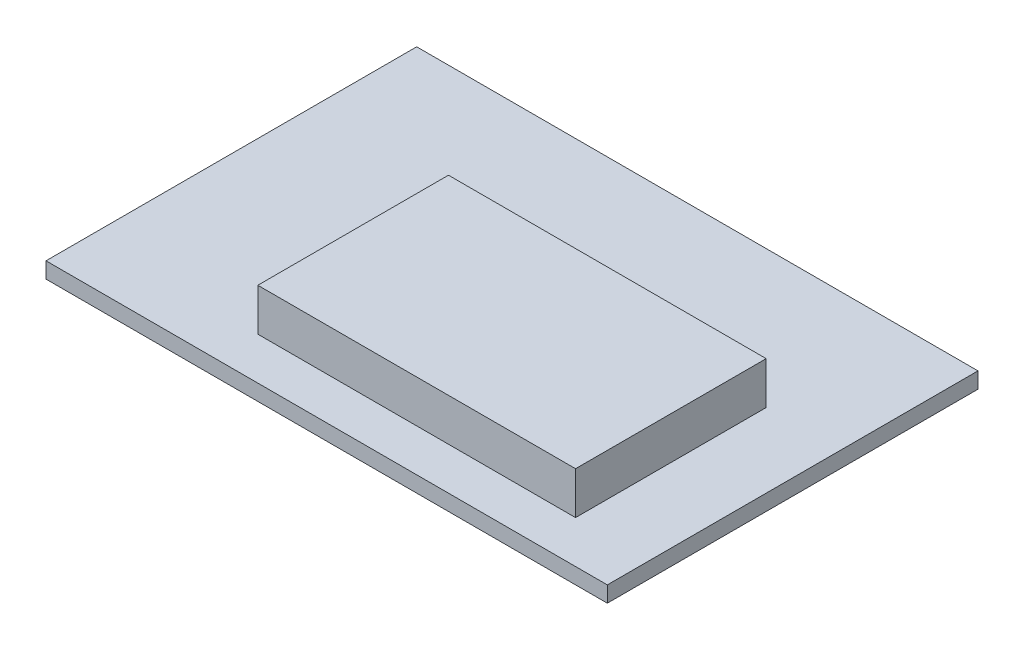
SolidWorks part; units mm, degrees
ref_plane "Frontal" through (0, 0, 0) normal (0, 0, 1) x (1, 0, 0)
ref_plane "Superior" through (0, 0, 0) normal (0, 1, 0) x (1, 0, 0)
ref_plane "Direito" through (0, 0, 0) normal (1, 0, 0) x (0, 0, -1)
sketch "Esboço1" plane through (0, 0, 0) normal (0, 1, 0) x (1, 0, 0)
  line L1 (-28.7306, 15.5259) -> (24.2694, 15.5259)
  line L2 (-28.7306, 15.5259) -> (-28.7306, -19.4741)
  line L3 (-28.7306, -19.4741) -> (24.2694, -19.4741)
  line L4 (24.2694, 15.5259) -> (24.2694, -19.4741)
  dimension "D1" = 35
  dimension "D2" = 53
extrude "Ressalto-extrusão1" add sketch "Esboço1" along normal blind 1.5
sketch "Esboço2" plane through (0, 1.5, 0) normal (0, 1, 0) x (1, 0, 0)
  line L0 (-28.7306, -19.4741) -> (24.2694, -19.4741) construction
  line L1 (-12.7306, 2.5259) -> (17.2694, 2.5259)
  line L2 (-12.7306, 2.5259) -> (-12.7306, -15.4741)
  line L3 (-12.7306, -15.4741) -> (17.2694, -15.4741)
  line L4 (17.2694, 2.5259) -> (17.2694, -15.4741)
  line L5 (24.2694, -19.4741) -> (24.2694, 15.5259) construction
  dimension "D1" = 30
  dimension "D2" = 18
  dimension "D3" = 4
  dimension "D4" = 7
extrude "Ressalto-extrusão2" add sketch "Esboço2" along normal blind 4
